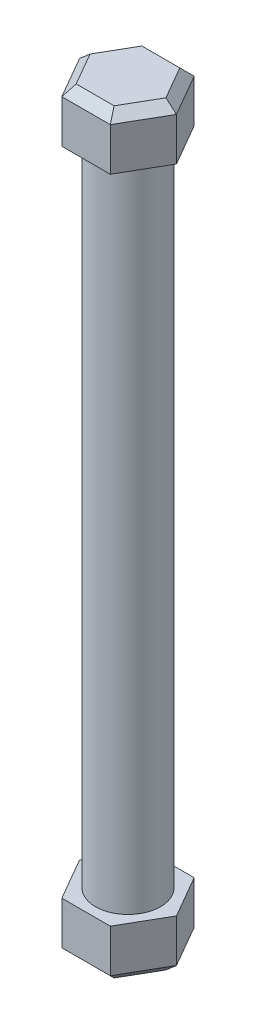
SolidWorks part; units mm, degrees
material "Zinc Alloy 7; AG40B; Zn-4Al-0.015Mg"
ref_plane "Front Plane" through (0, 0, 0) normal (0, 0, 1) x (1, 0, 0)
ref_plane "Top Plane" through (0, 0, 0) normal (0, 1, 0) x (1, 0, 0)
ref_plane "Right Plane" through (0, 0, 0) normal (1, 0, 0) x (0, 0, -1)
sketch "Sketch1" plane through (0, 0, 0) normal (0, 1, 0) x (1, 0, 0)
  circle A0 centre (0, 0) radius 2.5
  dimension "D1" = 5
extrude "Boss-Extrude1" add sketch "Sketch1" along normal blind 50
sketch "Sketch2" plane through (0, 50, 0) normal (0, 1, 0) x (1, 0, 0)
  line L1 (3.72, 0) -> (1.86, 3.2216)
  line L2 (1.86, 3.2216) -> (-1.86, 3.2216)
  line L3 (-1.86, 3.2216) -> (-3.72, 0)
  line L4 (-3.72, 0) -> (-1.86, -3.2216)
  line L5 (-1.86, -3.2216) -> (1.86, -3.2216)
  line L6 (1.86, -3.2216) -> (3.72, 0)
  circle A0 centre (0, 0) radius 3.2216 construction
extrude "Boss-Extrude2" add sketch "Sketch2" along normal blind 4
chamfer "Chamfer1" distance 0.7 angle 45 6 edges at (0, 54, 3.2216) (-2.79, 54, 1.6108) (-2.79, 54, -1.6108) (0, 54, -3.2216) (2.79, 54, -1.6108) (2.79, 54, 1.6108)
sketch "Sketch3" plane through (0, 0, 0) normal (0, -1, 0) x (1, 0, 0)
  line L1 (3.72, 0) -> (1.86, 3.2216)
  line L2 (1.86, 3.2216) -> (-1.86, 3.2216)
  line L3 (-1.86, 3.2216) -> (-3.72, 0)
  line L4 (-3.72, 0) -> (-1.86, -3.2216)
  line L5 (-1.86, -3.2216) -> (1.86, -3.2216)
  line L6 (1.86, -3.2216) -> (3.72, 0)
  circle A0 centre (0, 0) radius 3.2216 construction
extrude "Boss-Extrude3" add sketch "Sketch3" along normal blind 4
chamfer "Chamfer2" distance 0.7 angle 45 6 edges at (0, -4, -3.2216) (-2.79, -4, -1.6108) (-2.79, -4, 1.6108) (0, -4, 3.2216) (2.79, -4, 1.6108) (2.79, -4, -1.6108)
